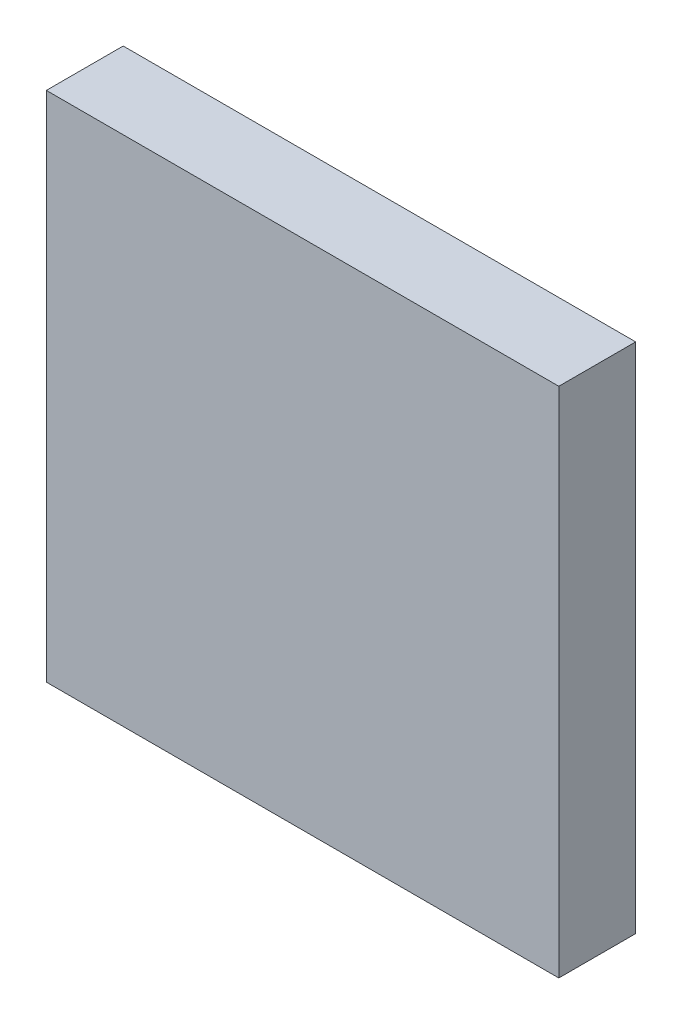
SolidWorks part; units mm, degrees
ref_plane "Front Plane" through (0, 0, 0) normal (0, 0, 1) x (1, 0, 0)
ref_plane "Top Plane" through (0, 0, 0) normal (0, 1, 0) x (1, 0, 0)
ref_plane "Right Plane" through (0, 0, 0) normal (1, 0, 0) x (0, 0, -1)
sketch "Sketch1" plane through (0, 0, 0) normal (0, 0, 1) x (1, 0, 0)
  line L1 (0, 0) -> (20, 0)
  line L2 (0, 0) -> (0, 20)
  line L3 (0, 20) -> (20, 20)
  line L4 (20, 0) -> (20, 20)
  dimension "D1" = 20
  dimension "D2" = 20
extrude "Boss-Extrude1" add sketch "Sketch1" along normal blind 3
